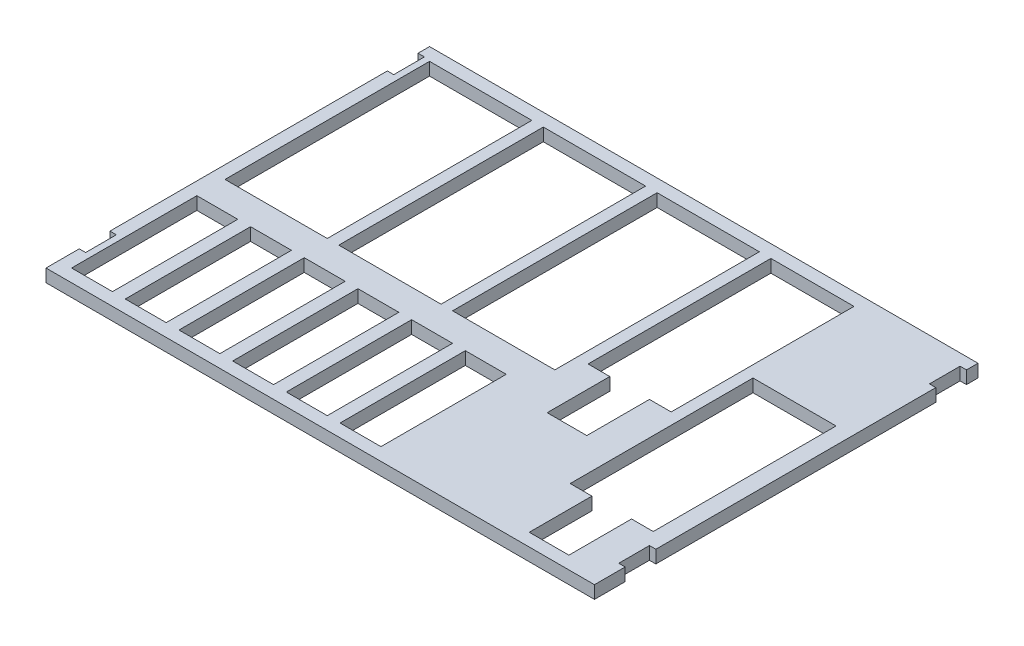
SolidWorks part; units mm, degrees
ref_plane "Front Plane" through (0, 0, 0) normal (0, 0, 1) x (1, 0, 0)
ref_plane "Top Plane" through (0, 0, 0) normal (0, 1, 0) x (1, 0, 0)
ref_plane "Right Plane" through (0, 0, 0) normal (1, 0, 0) x (0, 0, -1)
sketch "Sketch1" plane through (0, 0, 0) normal (0, 1, 0) x (1, 0, 0)
  line L1 (-214.5, 150) -> (214.5, 150)
  line L2 (-214.5, 150) -> (-214.5, -150)
  line L3 (-214.5, -150) -> (214.5, -150)
  line L4 (214.5, 150) -> (214.5, -150)
  line L5 (-214.5, 150) -> (214.5, -150) construction
  line L6 (-214.5, -150) -> (214.5, 150) construction
  point P0 (0, 0)
  dimension "D1" = 429
  dimension "D2" = 300
extrude "Boss-Extrude1" add sketch "Sketch1" against normal blind 10
sketch "Sketch2" plane through (0, 0, 0) normal (0, 1, 0) x (1, 0, 0)
  line L0 (214.5, 150) -> (-214.5, 150) construction
  line L1 (-204.5, 140) -> (-124.5, 140)
  line L2 (-204.5, 140) -> (-204.5, -20)
  line L3 (-204.5, -20) -> (-124.5, -20)
  line L4 (-124.5, 140) -> (-124.5, -20)
  line L5 (-214.5, 150) -> (-214.5, -150) construction
  line L6 (-115.5, 140) -> (-35.5, 140)
  line L7 (-115.5, 140) -> (-115.5, -20)
  line L8 (-115.5, -20) -> (-35.5, -20)
  line L9 (-35.5, 140) -> (-35.5, -20)
  line L10 (-26.5, 140) -> (53.5, 140)
  line L11 (-26.5, 140) -> (-26.5, -20)
  line L12 (-26.5, -20) -> (53.5, -20)
  line L13 (53.5, 140) -> (53.5, -20)
  line L15 (62.5, 140) -> (127.5, 140)
  line L16 (62.5, 140) -> (62.5, -3)
  line L17 (79.5, -52) -> (110.5, -52)
  line L18 (127.5, 140) -> (127.5, -3)
  line L22 (-214.5, -150) -> (214.5, -150) construction
  line L23 (-162.5, -42) -> (-162.5, -140)
  line L24 (-204.5, -42) -> (-172.5, -42)
  line L25 (-204.5, -42) -> (-204.5, -140)
  line L26 (-204.5, -140) -> (-172.5, -140)
  line L27 (-172.5, -42) -> (-172.5, -140)
  line L28 (-162.5, -42) -> (-130.5, -42)
  line L29 (-130.5, -42) -> (-130.5, -140)
  line L30 (-162.5, -140) -> (-130.5, -140)
  line L31 (-120.5, -42) -> (-120.5, -140)
  line L32 (-120.5, -42) -> (-88.5, -42)
  line L33 (-88.5, -42) -> (-88.5, -140)
  line L34 (-120.5, -140) -> (-88.5, -140)
  line L35 (-78.5, -42) -> (-78.5, -140)
  line L36 (-78.5, -42) -> (-46.5, -42)
  line L37 (-46.5, -42) -> (-46.5, -140)
  line L38 (-78.5, -140) -> (-46.5, -140)
  line L39 (-36.5, -42) -> (-36.5, -140)
  line L40 (-36.5, -42) -> (-4.5, -42)
  line L41 (-4.5, -42) -> (-4.5, -140)
  line L42 (-36.5, -140) -> (-4.5, -140)
  line L43 (5.5, -42) -> (5.5, -140)
  line L44 (5.5, -42) -> (37.5, -42)
  line L45 (37.5, -42) -> (37.5, -140)
  line L46 (5.5, -140) -> (37.5, -140)
  line L47 (184.5, -140) -> (153.5, -140)
  line L48 (201.5, -91) -> (201.5, 52)
  line L49 (201.5, 52) -> (136.5, 52)
  line L50 (136.5, -91) -> (136.5, 52)
  line L52 (79.5, -52) -> (110.5, -52)
  line L53 (79.5, -52) -> (79.5, -3)
  line L54 (62.5, -3) -> (79.5, -3)
  line L55 (110.5, -52) -> (110.5, -3)
  line L57 (110.5, -3) -> (127.5, -3)
  line L58 (153.5, -91) -> (136.5, -91)
  line L59 (153.5, -140) -> (184.5, -140)
  line L60 (153.5, -140) -> (153.5, -91)
  line L62 (184.5, -140) -> (184.5, -91)
  line L63 (184.5, -91) -> (201.5, -91)
  line L64 (-214.5, 117) -> (-209.5, 117)
  line L69 (0, 0) -> (0, -164.7907) construction
  line L79 (214.5, -150) -> (214.5, 150) construction
  line L80 (214.5, -102) -> (209.5, -102)
  line L81 (214.5, -102) -> (214.5, -126)
  line L82 (214.5, -126) -> (209.5, -126)
  line L83 (209.5, -102) -> (209.5, -126)
  line L84 (214.5, 141) -> (209.5, 141)
  line L89 (-214.5, -124) -> (-209.5, -124)
  line L90 (-214.5, -124) -> (-214.5, -100)
  line L91 (-214.5, -100) -> (-209.5, -100)
  line L92 (-209.5, -124) -> (-209.5, -100)
  line L94 (214.5, 117) -> (209.5, 117)
  line L95 (209.5, 141) -> (209.5, 117)
  line L96 (-209.5, 141) -> (-209.5, 117)
  line L97 (-214.5, 141) -> (-209.5, 141)
  line L98 (214.5, 117) -> (214.5, 141)
  line L99 (-214.5, 117) -> (-214.5, 141)
  dimension "D1" = 80
  dimension "D2" = 160
  dimension "D3" = 10
  dimension "D4" = 10
  dimension "D6" = 9
  dimension "D7" = 65
  dimension "D8" = 17
  dimension "D9" = 9
  dimension "D10" = 10
  dimension "D12" = 65
  dimension "D13" = 32
  dimension "D14" = 98
  dimension "D15" = 10
  dimension "D16" = 10
  dimension "D18" = 10
  dimension "D11" = 10
  dimension "D19" = 9
  dimension "D20" = 192
  dimension "D21" = 17
  dimension "D22" = 143
  dimension "D23" = 49
  dimension "D24" = 143
  dimension "D25" = 17
  dimension "D26" = 5
  dimension "D27" = 49
  dimension "D28" = 5
  dimension "D29" = 24
  dimension "D30" = 24
  dimension "D31" = 24
  dimension "D32" = 9
  dimension "D33" = 24
  dimension "D34" = 5
  dimension "D35" = 26
  dimension "D5" = 3
  dimension "D17" = 6
extrude "Cut-Extrude1" cut sketch "Sketch2" against normal blind 10
sketch "Sketch3" plane through (0, 0, 0) normal (0, 1, 0) x (1, 0, 0)
  line L0 (5.5, -140) -> (37.5, -140) construction
  line L1 (46.5, -60) -> (126.5, -60)
  line L2 (46.5, -60) -> (46.5, -140)
  line L3 (46.5, -140) -> (126.5, -140)
  line L4 (126.5, -60) -> (126.5, -140)
  line L8 (37.5, -42) -> (37.5, -140) construction
  dimension "D1" = 80
  dimension "D2" = 80
  dimension "D3" = 9
